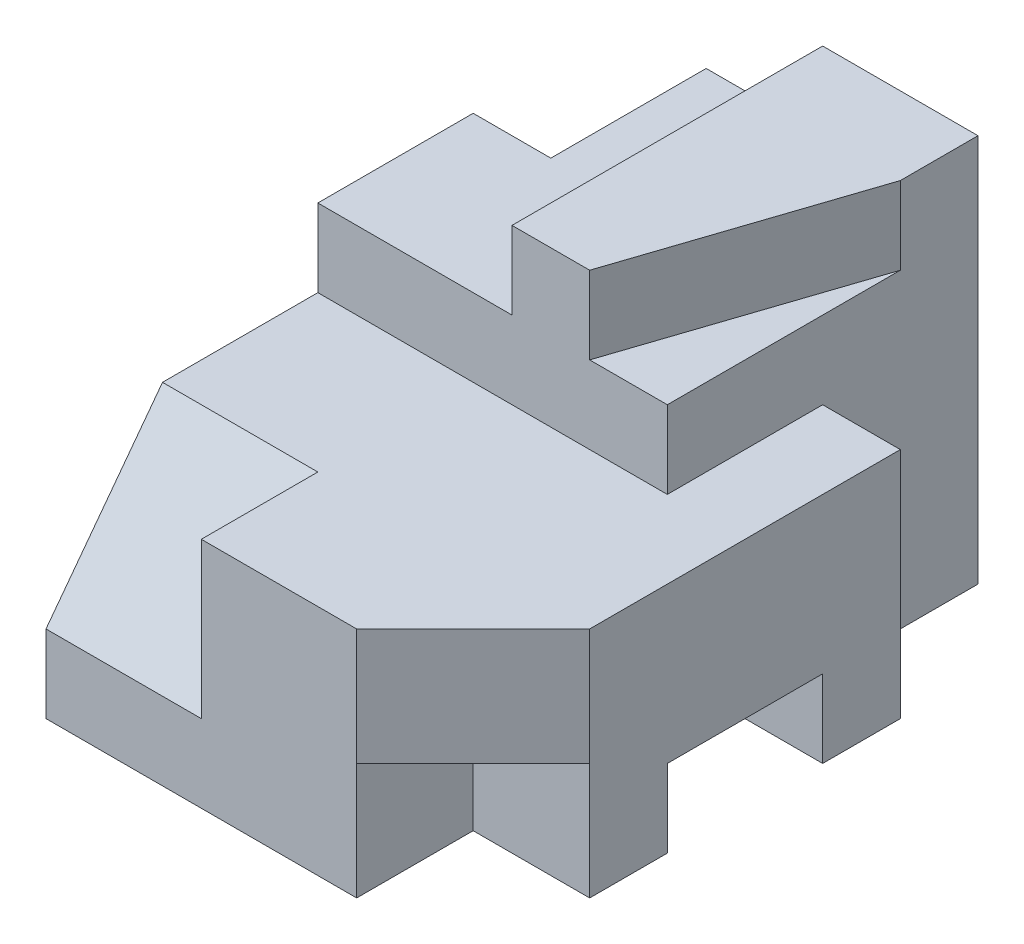
SolidWorks part; units mm, degrees
ref_plane "Front Plane" through (0, 0, 0) normal (0, 0, 1) x (1, 0, 0)
ref_plane "Top Plane" through (0, 0, 0) normal (0, 1, 0) x (1, 0, 0)
ref_plane "Right Plane" through (0, 0, 0) normal (1, 0, 0) x (0, 0, -1)
sketch "Sketch1" plane through (0, 0, 0) normal (0, 0, 1) x (1, 0, 0)
  line L1 (2.75, -2.5) -> (-2.75, -2.5)
  line L2 (2.75, -2.5) -> (2.75, 2.5)
  line L3 (2.75, 2.5) -> (-2.75, 2.5)
  line L4 (-2.75, -2.5) -> (-2.75, 2.5)
  line L5 (2.75, -2.5) -> (-2.75, 2.5) construction
  line L6 (2.75, 2.5) -> (-2.75, -2.5) construction
  point P0 (0, 0)
  dimension "D1" = 5.5
  dimension "D2" = 5
extrude "Boss-Extrude1" add sketch "Sketch1" along normal blind 7.5
sketch "Sketch2" plane through (-2.75, 0, 0) normal (-1, 0, 0) x (0, 0, 1)
  line L0 (6, 2.5) -> (7.5, -1.5)
  line L1 (7.5, 2.5) -> (0, 2.5) construction
  line L2 (7.5, 2.5) -> (7.5, -2.5) construction
  line L3 (7.5, -1.5) -> (7.5, 2.5)
  line L4 (7.5, 2.5) -> (6, 2.5)
  dimension "D1" = 1
  dimension "D2" = 1.5
extrude "Cut-Extrude1" cut sketch "Sketch2" against normal blind 2
sketch "Sketch3" plane through (2.75, 0, 0) normal (1, 0, 0) x (0, 0, -1)
  line L0 (0, -2.5) -> (-2, -2.5)
  line L1 (-7.5, -2.5) -> (0, -2.5) construction
  line L2 (-2, -2.5) -> (-2, 0.5)
  line L3 (-2, 0.5) -> (-4, 0.5)
  line L4 (-4, 0.5) -> (-4, 2.5)
  line L5 (-7.5, 2.5) -> (0, 2.5) construction
  line L6 (-4, 2.5) -> (0, 2.5)
  line L7 (0, 2.5) -> (0, -2.5)
  dimension "D1" = 3
  dimension "D2" = 2
  dimension "D3" = 2
extrude "Cut-Extrude2" cut sketch "Sketch3" against normal blind 1
sketch "Sketch4" plane through (0, 2.5, 0) normal (0, 1, 0) x (1, 0, 0)
  line L0 (2.75, -4) -> (2.75, -7.5)
  line L1 (2.75, -7.5) -> (-0.75, -7.5)
  line L2 (-0.75, -7.5) -> (-0.75, -6)
  line L3 (-0.75, -6) -> (-2.75, -6)
  line L4 (-2.75, -6) -> (-2.75, -4)
  line L5 (-2.75, -6) -> (-2.75, 0) construction
  line L6 (-2.75, -4) -> (1.75, -4)
  line L7 (1.75, -4) -> (1.75, -2) construction
  line L9 (1.75, -4) -> (2.75, -4)
  line M1 (2.75, -7.5) -> (2.75, -4)
  line M2 (2.75, -4) -> (1.75, -4)
  line M5 (-2.75, 0) -> (-2.75, -6)
  line M6 (-2.75, -6) -> (-0.75, -6)
  line M7 (-0.75, -6) -> (-0.75, -7.5)
  line M8 (-0.75, -7.5) -> (2.75, -7.5)
  dimension "D1" = 2
extrude "Cut-Extrude3" cut sketch "Sketch4" against normal blind 2 contours L6 M5 M6 M7 M8 M1 M2
sketch "Sketch5" plane through (-2.75, 0, 0) normal (-1, 0, 0) x (0, 0, 1)
  line L0 (6, 2.5) -> (6, 0.5)
  line L1 (6, 0.5) -> (7.5, -1.5)
  line L2 (7.5, -1.5) -> (6, 2.5)
extrude "Cut-Extrude4" cut sketch "Sketch5" against normal blind 2
sketch "Sketch6" plane through (0, 2.5, 0) normal (0, 1, 0) x (1, 0, 0)
  line L0 (1.75, -4) -> (1.75, -1)
  line L1 (1.75, 0) -> (1.75, -4) construction
  line L2 (1.75, -1) -> (0.75, -4)
  line L3 (-2.75, -4) -> (1.75, -4) construction
  line L4 (0.75, -4) -> (1.75, -4)
  line L5 (-2.75, -4) -> (-0.25, -4)
  line L6 (-0.25, -4) -> (-0.25, 0)
  line L7 (1.75, 0) -> (-2.75, 0) construction
  line L8 (-0.25, 0) -> (-2.75, 0)
  line L9 (-2.75, 0) -> (-2.75, -4)
  dimension "D1" = 1
  dimension "D2" = 1
  dimension "D3" = 2.5
extrude "Cut-Extrude5" cut sketch "Sketch6" against normal blind 1
sketch "Sketch7" plane through (0, 1.5, 0) normal (0, 1, 0) x (1, 0, 0)
  line L0 (-2.75, 0) -> (-1.75, 0)
  line L1 (-0.25, 0) -> (-2.75, 0) construction
  line L2 (-1.75, 0) -> (-1.75, -2)
  line L3 (-1.75, -2) -> (-2.75, -2)
  line L4 (-2.75, 0) -> (-2.75, -4) construction
  line L5 (-2.75, -2) -> (-2.75, 0)
  dimension "D1" = 1
  dimension "D2" = 2
extrude "Cut-Extrude6" cut sketch "Sketch7" against normal through all
sketch "Sketch8" plane through (2.75, 0, 0) normal (1, 0, 0) x (0, 0, -1)
  line L0 (-5, -2.5) -> (-5, -1.5)
  line L1 (-7.5, -2.5) -> (-2, -2.5) construction
  line L2 (-5, -1.5) -> (-3, -1.5)
  line L3 (-3, -1.5) -> (-3, -2.5)
  line L4 (-3, -2.5) -> (-5, -2.5)
  dimension "D1" = 1
  dimension "D2" = 2
  dimension "D3" = 1
extrude "Cut-Extrude7" cut sketch "Sketch8" against normal through all
sketch "Sketch10" plane through (0, 0.5, 0) normal (0, 1, 0) x (1, 0, 0)
  line L0 (2.75, -6) -> (1.25, -7.5)
  line L1 (2.75, -7.5) -> (2.75, -2) construction
  line L2 (-0.75, -7.5) -> (2.75, -7.5) construction
  line L3 (1.25, -7.5) -> (2.75, -7.5)
  line L4 (2.75, -7.5) -> (2.75, -6)
  dimension "D1" = 1.5
  dimension "D2" = 1.5
extrude "Cut-Extrude8" cut sketch "Sketch10" against normal through all
sketch "Sketch11" plane through (2.75, 0, 0) normal (1, 0, 0) x (0, 0, -1)
  line L0 (-6, -2.5) -> (-6, -1)
  line L1 (-6, -2.5) -> (-6, 0.5) construction
  line L2 (-6, -1) -> (-7.5, -1)
  line L3 (-7.5, -2.5) -> (-7.5, 0.5) construction
  line L4 (-7.5, -1) -> (-7.5, -2.5)
  line L5 (-7.5, -2.5) -> (-6, -2.5)
  dimension "D1" = 1.5
extrude "Cut-Extrude9" cut sketch "Sketch11" against normal blind 1.5
